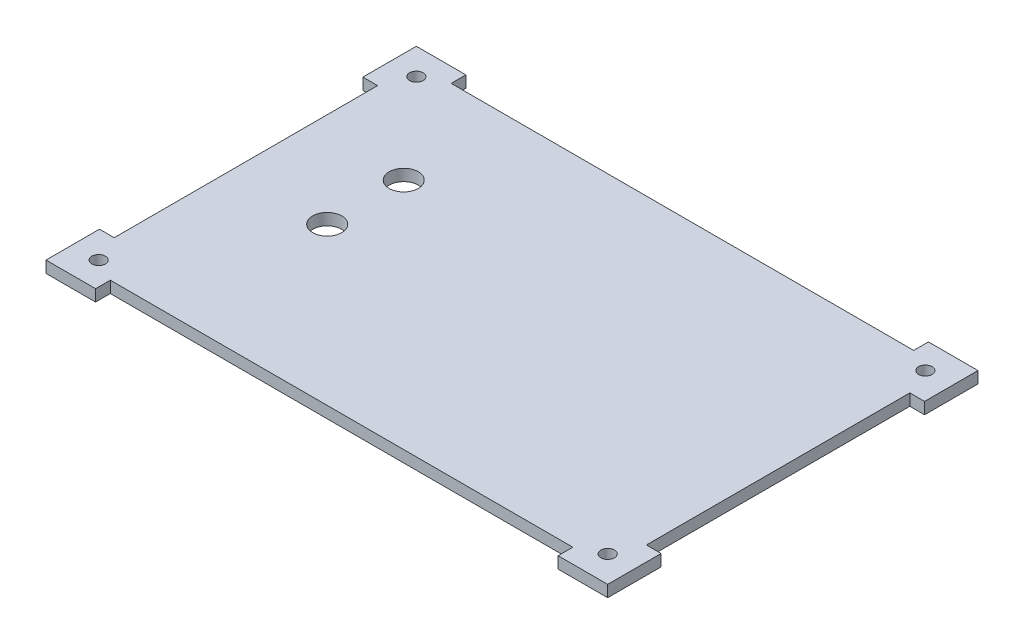
SolidWorks part; units mm, degrees
ref_plane "Front Plane" through (0, 0, 0) normal (0, 0, 1) x (1, 0, 0)
ref_plane "Top Plane" through (0, 0, 0) normal (0, 1, 0) x (1, 0, 0)
ref_plane "Right Plane" through (0, 0, 0) normal (1, 0, 0) x (0, 0, -1)
sketch "Sketch1" plane through (0, 0, 0) normal (0, 1, 0) x (1, 0, 0)
  line L1 (0, 0) -> (137.4, 0)
  line L2 (0, 0) -> (0, -88)
  line L3 (0, -88) -> (137.4, -88)
  line L4 (137.4, 0) -> (137.4, -88)
  dimension "D1" = 137.4
  dimension "D2" = 88
extrude "Boss-Extrude1" add sketch "Sketch1" along normal blind 3
sketch "Sketch2" plane through (0, 0, 0) normal (0, -1, 0) x (1, 0, 0)
  line L0 (0, 0) -> (0, 88) construction
  line L1 (0, 88) -> (137.4, 88) construction
  line L2 (137.4, 0) -> (0, 0) construction
  line L3 (137.4, 88) -> (137.4, 0) construction
  circle A0 centre (3, 85) radius 1.75
  circle A1 centre (134.4, 85) radius 1.75
  circle A2 centre (134.4, 3) radius 1.75
  circle A3 centre (3, 3) radius 1.75
  dimension "D1" = 3.5
  dimension "D2" = 3
  dimension "D3" = 3
  dimension "D4" = 3
  dimension "D5" = 3
  dimension "D6" = 3
  dimension "D7" = 3
  dimension "D8" = 3
  dimension "D9" = 3
extrude "Cut-Extrude1" cut sketch "Sketch2" against normal through all
sketch "Sketch3" plane through (0, 0, 0) normal (0, -1, 0) x (1, 0, 0)
  line L0 (0, 0) -> (0, 88) construction
  line L1 (-3.8, 91.8) -> (0, 91.8)
  line L2 (-3.8, 91.8) -> (-3.8, 78)
  line L3 (-3.8, 78) -> (0, 78)
  line L4 (0, 91.8) -> (0, 78)
  line L5 (0, 88) -> (137.4, 88) construction
  line L6 (0, 91.8) -> (9, 91.8)
  line L7 (0, 91.8) -> (0, 88)
  line L8 (0, 88) -> (9, 88)
  line L9 (9, 91.8) -> (9, 88)
  line L10 (137.4, 88) -> (137.4, 0) construction
  line L11 (137.4, 88) -> (128.4, 88)
  line L12 (137.4, 88) -> (137.4, 91.8)
  line L13 (137.4, 91.8) -> (128.4, 91.8)
  line L14 (128.4, 88) -> (128.4, 91.8)
  line L15 (137.4, 91.8) -> (141.2, 91.8)
  line L16 (137.4, 91.8) -> (137.4, 78)
  line L17 (137.4, 78) -> (141.2, 78)
  line L18 (141.2, 91.8) -> (141.2, 78)
  line L19 (137.4, 0) -> (0, 0) construction
  line L20 (0, 0) -> (-3.8, 0)
  line L21 (0, 0) -> (0, 10)
  line L22 (0, 10) -> (-3.8, 10)
  line L23 (-3.8, 0) -> (-3.8, 10)
  line L24 (-3.8, 0) -> (9, 0)
  line L25 (-3.8, 0) -> (-3.8, -3.8)
  line L26 (-3.8, -3.8) -> (9, -3.8)
  line L27 (9, 0) -> (9, -3.8)
  line L29 (137.4, 0) -> (141.2, 0)
  line L30 (137.4, 0) -> (137.4, 10)
  line L31 (137.4, 10) -> (141.2, 10)
  line L32 (141.2, 0) -> (141.2, 10)
  line L33 (141.2, 0) -> (128.4, 0)
  line L34 (141.2, 0) -> (141.2, -3.8)
  line L35 (141.2, -3.8) -> (128.4, -3.8)
  line L36 (128.4, 0) -> (128.4, -3.8)
  line M11 (0, 88) -> (0, 0)
  line M12 (0, 0) -> (137.4, 0)
  line M13 (137.4, 0) -> (137.4, 88)
  line M14 (137.4, 88) -> (0, 88)
  dimension "D1" = 10
  dimension "D2" = 9
  dimension "D3" = 3.8
  dimension "D4" = 3.8
  dimension "D5" = 3.8
  dimension "D6" = 3.8
  dimension "D7" = 9
  dimension "D8" = 10
  dimension "D9" = 3.8
  dimension "D10" = 3.8
  dimension "D11" = 10
  dimension "D12" = 9
  dimension "D13" = 3.8
  dimension "D14" = 3.8
  dimension "D15" = 10
  dimension "D16" = 9
extrude "Boss-Extrude2" add sketch "Sketch3" against normal through all contours L4 L1 L2 L3 M11 | L9 L6 L4 M14 | L23 L20 L22 M11 | L27 L20 L25 L26 M12 | L36 L35 L34 L29 M12 | L29 L32 L31 M13 | L14 L12 L13 M14 | L18 L15 L12 L17 M13
sketch "Sketch4" plane through (0, 0, 0) normal (0, -1, 0) x (1, 0, 0)
  line L0 (0, 10) -> (0, 78) construction
  line L1 (9, 88) -> (128.4, 88) construction
  circle A0 centre (24.5, 47.5) radius 3.75
  circle A1 centre (24.5, 27.75) radius 3.75
  dimension "D1" = 7.5
  dimension "D2" = 7.5
  dimension "D3" = 24.5
  dimension "D4" = 40.5
  dimension "D5" = 24.5
  dimension "D6" = 19.75
extrude "Cut-Extrude2" cut sketch "Sketch4" against normal through all
equation "\"D4@Sketch2\"=\"D2@Sketch2\""
equation "\"D5@Sketch2\"=\"D4@Sketch2\""
equation "\"D6@Sketch2\"=\"D5@Sketch2\""
equation "\"D7@Sketch2\"=\"D6@Sketch2\""
equation "\"D8@Sketch2\"=\"D2@Sketch2\""
equation "\"D9@Sketch2\"=\"D8@Sketch2\""
equation "\"D2@Sketch4\"=\"D1@Sketch4\""
equation "\"D5@Sketch4\"=\"D3@Sketch4\""
equation "\"D9@Sketch3\"=\"D3@Sketch3\""
equation "\"D4@Sketch3\"=\"D5@Sketch3\""
equation "\"D10@Sketch3\"=\"D5@Sketch3\""
equation "\"D14@Sketch3\"=\"D5@Sketch3\""
equation "\"D13@Sketch3\"=\"D6@Sketch3\""
